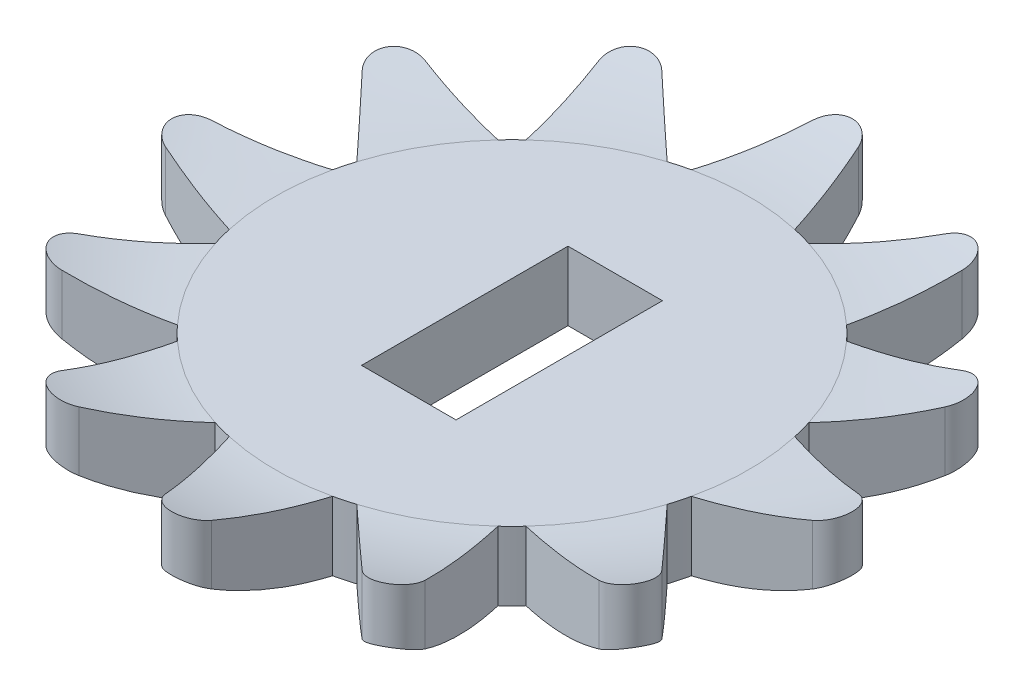
SolidWorks part; units mm, degrees
material "1060 Alloy"
ref_plane "Front Plane" through (0, 0, 0) normal (0, 0, 1) x (1, 0, 0)
ref_plane "Top Plane" through (0, 0, 0) normal (0, 1, 0) x (1, 0, 0)
ref_plane "Right Plane" through (0, 0, 0) normal (1, 0, 0) x (0, 0, -1)
sketch "Sketch1" plane through (0, 0, 0) normal (0, 1, 0) x (1, 0, 0)
  line L2 (0, 9.18) -> (0, 4.2387) construction
  line L6 (1.5, 6.7094) -> (0.6685, 9.3876)
  line L7 (-1.5, 6.7094) -> (-0.6685, 9.3876)
  line L8 (2.0556, 6.5605) -> (4.1148, 8.4641)
  line L9 (4.6537, 5.0605) -> (5.2727, 7.7956)
  line L11 (5.0605, 4.6537) -> (7.7956, 5.2727)
  line L12 (6.5605, 2.0556) -> (8.4641, 4.1148)
  line L14 (6.7094, 1.5) -> (9.3876, 0.6685)
  line L15 (6.7094, -1.5) -> (9.3876, -0.6685)
  line L17 (6.5605, -2.0556) -> (8.4641, -4.1148)
  line L18 (5.0605, -4.6537) -> (7.7956, -5.2727)
  line L20 (4.6537, -5.0605) -> (5.2727, -7.7956)
  line L21 (2.0556, -6.5605) -> (4.1148, -8.4641)
  line L23 (1.5, -6.7094) -> (0.6685, -9.3876)
  line L24 (-1.5, -6.7094) -> (-0.6685, -9.3876)
  line L26 (-2.0556, -6.5605) -> (-4.1148, -8.4641)
  line L27 (-4.6537, -5.0605) -> (-5.2727, -7.7956)
  line L29 (-5.0605, -4.6537) -> (-7.7956, -5.2727)
  line L30 (-6.5605, -2.0556) -> (-8.4641, -4.1148)
  line L32 (-6.7094, -1.5) -> (-9.3876, -0.6685)
  line L33 (-6.7094, 1.5) -> (-9.3876, 0.6685)
  line L35 (-6.5605, 2.0556) -> (-8.4641, 4.1148)
  line L36 (-5.0605, 4.6537) -> (-7.7956, 5.2727)
  line L38 (-4.6537, 5.0605) -> (-5.2727, 7.7956)
  line L39 (-2.0556, 6.5605) -> (-4.1148, 8.4641)
  line L40 (0, 0) -> (0, 1.905) construction
  line L41 (0, 0) -> (-4.13, 0) construction
  line L42 (0, 0) -> (4.13, 0) construction
  arc A3 (-6.7094, -1.5) -> (-6.5605, -2.0556) centre (0, 0) ccw
  arc A4 (0.6685, 9.3876) -> (-0.6685, 9.3876) centre (0, 9.18) ccw
  arc A5 (5.2727, 7.7956) -> (4.1148, 8.4641) centre (4.59, 7.9501) ccw
  arc A6 (8.4641, 4.1148) -> (7.7956, 5.2727) centre (7.9501, 4.59) ccw
  arc A7 (9.3876, -0.6685) -> (9.3876, 0.6685) centre (9.18, 0) ccw
  arc A8 (7.7956, -5.2727) -> (8.4641, -4.1148) centre (7.9501, -4.59) ccw
  arc A9 (4.1148, -8.4641) -> (5.2727, -7.7956) centre (4.59, -7.9501) ccw
  arc A10 (-0.6685, -9.3876) -> (0.6685, -9.3876) centre (0, -9.18) ccw
  arc A11 (-5.2727, -7.7956) -> (-4.1148, -8.4641) centre (-4.59, -7.9501) ccw
  arc A12 (-8.4641, -4.1148) -> (-7.7956, -5.2727) centre (-7.9501, -4.59) ccw
  arc A13 (-9.3876, 0.6685) -> (-9.3876, -0.6685) centre (-9.18, 0) ccw
  arc A14 (-7.7956, 5.2727) -> (-8.4641, 4.1148) centre (-7.9501, 4.59) ccw
  arc A15 (-4.1148, 8.4641) -> (-5.2727, 7.7956) centre (-4.59, 7.9501) ccw
  arc A16 (-6.5605, 2.0556) -> (-6.7094, 1.5) centre (0, 0) ccw
  arc A17 (-4.6537, 5.0605) -> (-5.0605, 4.6537) centre (0, 0) ccw
  arc A18 (-1.5, 6.7094) -> (-2.0556, 6.5605) centre (0, 0) ccw
  arc A19 (2.0556, 6.5605) -> (1.5, 6.7094) centre (0, 0) ccw
  arc A20 (5.0605, 4.6537) -> (4.6537, 5.0605) centre (0, 0) ccw
  arc A21 (6.7094, 1.5) -> (6.5605, 2.0556) centre (0, 0) ccw
  arc A22 (6.5605, -2.0556) -> (6.7094, -1.5) centre (0, 0) ccw
  arc A23 (4.6537, -5.0605) -> (5.0605, -4.6537) centre (0, 0) ccw
  arc A24 (1.5, -6.7094) -> (2.0556, -6.5605) centre (0, 0) ccw
  arc A25 (-2.0556, -6.5605) -> (-1.5, -6.7094) centre (0, 0) ccw
  arc A26 (-5.0605, -4.6537) -> (-4.6537, -5.0605) centre (0, 0) ccw
  point P73 (0, 0)
  dimension "D3" = 13.75
  dimension "D5" = 1.4
  dimension "D4" = 3
  dimension "D6" = 12
extrude "Boss-Extrude1" add sketch "Sketch1" along normal blind 2.45
sketch "Sketch7" plane through (0, 0, 0) normal (0, 0, 1) x (1, 0, 0)
  line L0 (0, 2.45) -> (-6.875, 2.45)
  line L1 (0.6685, 2.45) -> (-0.6685, 2.45) construction
  line L2 (-7.7956, 2.45) -> (-5.0605, 2.45) construction
  line L3 (-6.875, 2.45) -> (-9.88, 2.45)
  line L4 (-6.875, 0) -> (-4.1148, 0)
  line L5 (-6.875, 2) -> (-6.875, 2.45)
  line L6 (-7.7956, 0) -> (-5.0605, 0) construction
  line L7 (-6.875, 2) -> (0, 2)
  line L8 (0, 2) -> (0, 2.45)
  line L9 (-6.875, 2.45) -> (-9.88, 2.45)
  line L10 (-9.88, 2.45) -> (-9.88, 0) construction
  line L11 (-6.875, 2) -> (-6.875, 0)
  line L12 (-9.88, 0.85) -> (-9.88, 0)
  line L13 (-9.88, 0) -> (-6.875, 0)
  line L14 (0, 0) -> (0, 4.3852) construction
  arc A0 (-6.875, 0) -> (-9.88, 0.85) centre (-6.875, 5.7368) cw
  arc A1 (-6.875, 2) -> (-9.88, 2.45) centre (-6.875, 12.2584) cw
  dimension "D1" = 6.875
  dimension "D2" = 2
  dimension "D3" = 1.6
revolve "Cut-Revolve2" cut sketch "Sketch7" angle 360 about L14
sketch "Sketch8" plane through (0, 2, 0) normal (0, 1, 0) x (1, 0, 0)
  line L1 (-1.3716, 2.9972) -> (1.3716, 2.9972)
  line L2 (-1.3716, 2.9972) -> (-1.3716, -2.9972)
  line L3 (-1.3716, -2.9972) -> (1.3716, -2.9972)
  line L4 (1.3716, 2.9972) -> (1.3716, -2.9972)
  point P4 (-1.3716, 0)
  point P6 (0, 2.9972)
  dimension "D1" = 2.7432
  dimension "D2" = 5.9944
extrude "Cut-Extrude1" cut sketch "Sketch8" against normal blind 10
